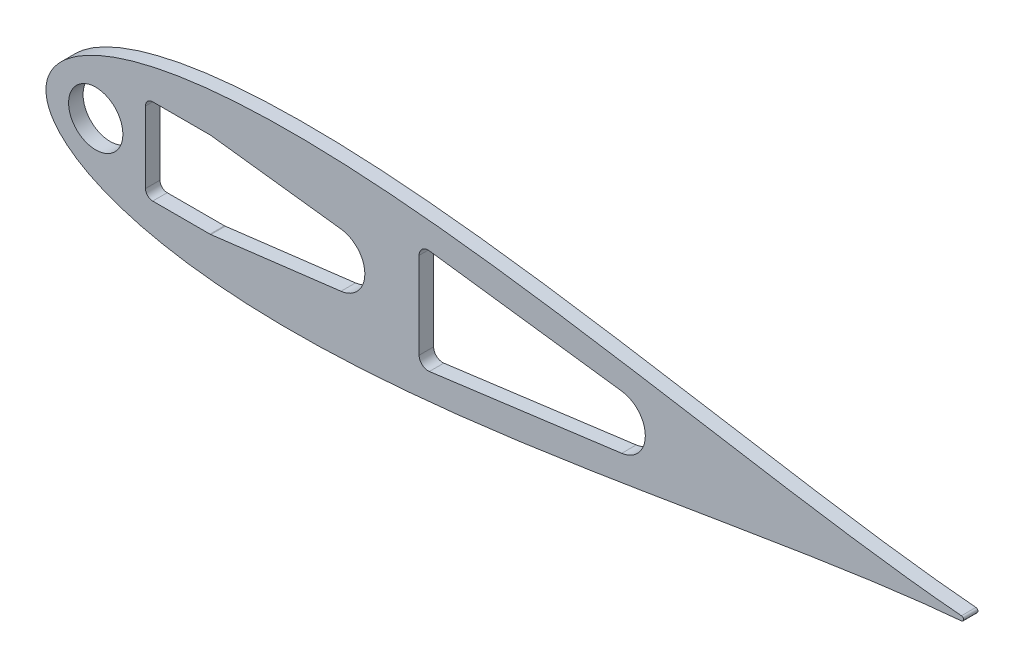
SolidWorks part; units mm, degrees
ref_plane "Front Plane" through (0, 0, 0) normal (0, 0, 1) x (1, 0, 0)
ref_plane "Top Plane" through (0, 0, 0) normal (0, 1, 0) x (1, 0, 0)
ref_plane "Right Plane" through (0, 0, 0) normal (1, 0, 0) x (0, 0, -1)
curve "Curve4"
  spline degree 3 poles (100, 0, 0) (99.8498, 0.0023, 0) (99.4759, 0.008, 0) (99.1023, 0.0238, 0) (98.8789, 0.0332, 0) knots 0 0 0 0 0.401829 1 1 1 1
curve "Curve5"
  spline degree 3 poles (99.3714, -0.0082, 0) (100.2526, 0, 0) (99.3714, 0.0082, 0) (98.8504, 0.035, 0) (97.904, 0.0811, 0) (96.8285, 0.1543, 0) (95.5159, 0.2583, 0) (94.013, 0.3972, 0) (92.313, 0.574, 0) (90.4281, 0.791, 0) (88.3655, 1.0495, 0) (86.1348, 1.3497, 0) (83.7456, 1.691, 0) (81.2082, 2.0715, 0) (78.5335, 2.4886, 0) (75.7326, 2.9386, 0) (72.8172, 3.4168, 0) (69.799, 3.9177, 0) (66.6904, 4.435, 0) (63.5039, 4.9616, 0) (60.2521, 5.4899, 0) (56.948, 6.0119, 0) (53.6049, 6.519, 0) (50.2363, 7.0024, 0) (46.8558, 7.4534, 0) (43.4774, 7.8632, 0) (40.1152, 8.2232, 0) (36.7837, 8.5249, 0) (33.4975, 8.7606, 0) (30.2716, 8.923, 0) (27.1211, 9.0055, 0) (24.0614, 9.0025, 0) (21.108, 8.909, 0) (18.277, 8.7213, 0) (15.5843, 8.4369, 0) (13.0466, 8.0543, 0) (10.6806, 7.5735, 0) (8.5039, 6.996, 0) (6.5349, 6.3253, 0) (4.7933, 5.5673, 0) (3.3001, 4.7321, 0) (2.0777, 3.8366, 0) (1.1467, 2.91, 0) (0.5165, 2.0014, 0) (0.165, 1.1816, 0) (0.0231, 0.524, 0) (-0.0093, 0, 0) (0.0231, -0.524, 0) (0.165, -1.1816, 0) (0.5165, -2.0014, 0) (1.1467, -2.91, 0) (2.0777, -3.8366, 0) (3.3001, -4.7321, 0) (4.7933, -5.5673, 0) (6.5349, -6.3253, 0) (8.5039, -6.996, 0) (10.6806, -7.5735, 0) (13.0466, -8.0543, 0) (15.5843, -8.4369, 0) (18.277, -8.7213, 0) (21.108, -8.909, 0) (24.0614, -9.0025, 0) (27.1211, -9.0055, 0) (30.2716, -8.923, 0) (33.4975, -8.7606, 0) (36.7837, -8.5249, 0) (40.1152, -8.2232, 0) (43.4774, -7.8632, 0) (46.8558, -7.4534, 0) (50.2363, -7.0024, 0) (53.6049, -6.519, 0) (56.948, -6.0119, 0) (60.2521, -5.4899, 0) (63.5039, -4.9616, 0) (66.6904, -4.435, 0) (69.799, -3.9177, 0) (72.8172, -3.4168, 0) (75.7326, -2.9386, 0) (78.5335, -2.4886, 0) (81.2082, -2.0715, 0) (83.7456, -1.691, 0) (86.1348, -1.3497, 0) (88.3655, -1.0495, 0) (90.4281, -0.791, 0) (92.313, -0.574, 0) (94.013, -0.3972, 0) (95.5159, -0.2583, 0) (96.8285, -0.1543, 0) (97.904, -0.0811, 0) (98.8504, -0.035, 0) (99.3714, -0.0082, 0) (100.2526, 0, 0) (99.3714, 0.0082, 0) knots -0.009667 -0.005395 -0.002168 0 0.002168 0.005395 0.009667 0.014967 0.021271 0.028553 0.036781 0.04592 0.055932 0.066773 0.078397 0.090755 0.103793 0.117456 0.131686 0.146422 0.1616 0.177156 0.193024 0.209135 0.225421 0.241812 0.258238 0.274629 0.290914 0.307025 0.322893 0.338448 0.353626 0.368361 0.38259 0.396253 0.40929 0.421647 0.43327 0.444109 0.454119 0.463255 0.471479 0.478755 0.485052 0.490344 0.49461 0.497833 0.5 0.502167 0.50539 0.509656 0.514948 0.521245 0.528521 0.536745 0.545881 0.555891 0.56673 0.578353 0.59071 0.603747 0.61741 0.631639 0.646374 0.661552 0.677107 0.692975 0.709086 0.725371 0.741762 0.758188 0.774579 0.790865 0.806976 0.822844 0.8384 0.853578 0.868314 0.882544 0.896207 0.909245 0.921603 0.933227 0.944068 0.95408 0.963219 0.971447 0.978729 0.985033 0.990333 0.994605 0.997832 1 1.002168 1.005395 1.009667 periodic
sketch "Sketch2" plane through (0, 0, 0) normal (0, 0, 1) x (1, 0, 0)
  line L0 (642.3793, 0) -> (0, 0) construction
  circle A14 centre (642.3793, 0) radius 1.5875 construction
  arc A15 (642.5108, -1.582) -> (642.5108, 1.582) centre (642.3793, 0) ccw
  spline S2 degree 3 poles (666.3448, -0.0547) (672.2538, 0) (666.3448, 0.0547) (662.8509, 0.2344) (656.505, 0.5436) (649.293, 1.0348) (640.4916, 1.7319) (630.4138, 2.6634) (619.0141, 3.8493) (606.375, 5.3044) (592.5439, 7.0376) (577.5855, 9.0506) (561.5643, 11.3389) (544.5497, 13.8907) (526.6141, 16.6877) (507.8326, 19.7051) (488.2827, 22.9117) (468.0444, 26.2704) (447.1994, 29.739) (425.8316, 33.2703) (404.0263, 36.8132) (381.8707, 40.3133) (359.4533, 43.7135) (336.8645, 46.9554) (314.1962, 49.9798) (291.5418, 52.7277) (268.9963, 55.1412) (246.6566, 57.1646) (224.6209, 58.7452) (202.9892, 59.8341) (181.8631, 60.3875) (161.3458, 60.367) (141.542, 59.7399) (122.5581, 58.4818) (104.5023, 56.5743) (87.485, 54.0089) (71.6197, 50.7848) (57.0237, 46.9125) (43.8205, 42.415) (32.1416, 37.3322) (22.1291, 31.7315) (13.9324, 25.7264) (7.6896, 19.5132) (3.4631, 13.4204) (1.1063, 7.9234) (0.1546, 3.5138) (-0.0622, 0) (0.1546, -3.5138) (1.1063, -7.9234) (3.4631, -13.4204) (7.6896, -19.5132) (13.9324, -25.7264) (22.1291, -31.7315) (32.1416, -37.3322) (43.8205, -42.415) (57.0237, -46.9125) (71.6197, -50.7848) (87.485, -54.0089) (104.5023, -56.5743) (122.5581, -58.4818) (141.542, -59.7399) (161.3458, -60.367) (181.8631, -60.3875) (202.9892, -59.8341) (224.6209, -58.7452) (246.6566, -57.1646) (268.9963, -55.1412) (291.5418, -52.7277) (314.1962, -49.9798) (336.8645, -46.9554) (359.4533, -43.7135) (381.8707, -40.3133) (404.0263, -36.8132) (425.8316, -33.2703) (447.1994, -29.739) (468.0444, -26.2704) (488.2827, -22.9117) (507.8326, -19.7051) (526.6141, -16.6877) (544.5497, -13.8907) (561.5643, -11.3389) (577.5855, -9.0506) (592.5439, -7.0376) (606.375, -5.3044) (619.0141, -3.8493) (630.4138, -2.6634) (640.4916, -1.7319) (649.293, -1.0348) (656.505, -0.5436) (662.8509, -0.2344) (666.3448, -0.0547) (672.2538, 0) (666.3448, 0.0547) knots -0.009667 -0.005395 -0.002168 0 0.002168 0.005395 0.009667 0.014967 0.021271 0.028553 0.036781 0.04592 0.055932 0.066773 0.078397 0.090755 0.103793 0.117456 0.131686 0.146422 0.1616 0.177156 0.193024 0.209135 0.225421 0.241812 0.258238 0.274629 0.290914 0.307025 0.322893 0.338448 0.353626 0.368361 0.38259 0.396253 0.40929 0.421647 0.43327 0.444109 0.454119 0.463255 0.471479 0.478755 0.485052 0.490344 0.49461 0.497833 0.5 0.502167 0.50539 0.509656 0.514948 0.521245 0.528521 0.536745 0.545881 0.555891 0.56673 0.578353 0.59071 0.603747 0.61741 0.631639 0.646374 0.661552 0.677107 0.692975 0.709086 0.725371 0.741762 0.758188 0.774579 0.790865 0.806976 0.822844 0.8384 0.853578 0.868314 0.882544 0.896207 0.909245 0.921603 0.933227 0.944068 0.95408 0.963219 0.971447 0.978729 0.985033 0.990333 0.994605 0.997832 1 1.002168 1.005395 1.009667 only from (670.56, 0) to (670.56, 0)
  point P8 (1.2169, -4.6585)
  point P10 (1.2169, 4.6585)
  dimension "D10" = 3.175
extrude "Boss-Extrude1" add sketch "Sketch2" along normal blind 5.4737
extrude "Cut-Extrude4" cut sketch "Sketch7" against normal through all
sketch "Sketch7" plane through (327.9592, -13.7514, 6.35) normal (0, 0, 1) x (1, 0, 0)
  line L1 (-154.9852, -16.7286) -> (-66.0852, -16.7286)
  line L2 (-154.9852, -16.7286) -> (-154.9852, 44.2314)
  line L3 (-154.9852, 44.2314) -> (-66.0852, 44.2314)
  line L4 (-66.0852, -16.7286) -> (-66.0852, 44.2314)
  line L5 (-154.9852, -16.7286) -> (-66.0852, 44.2314) construction
  line L6 (-154.9852, 44.2314) -> (-66.0852, -16.7286) construction
  point P0 (-110.5352, 13.7514)
extrude "Cut-Extrude5" cut sketch "Sketch8" against normal through all
sketch "Sketch8" plane through (327.9592, -13.7514, 6.35) normal (0, 0, 1) x (1, 0, 0)
  circle A0 centre (314.9285, 13.7514) radius 1.2446
scale "Scale1" bodies to scale 101 scale about origin uniform scaling yes scale factor 0.5
sketch "Sketch11" plane through (0, 0, 0) normal (0, 0, -1) x (-1, 0, 0)
  arc A1 (-321.2554, 0.791) -> (-321.2554, -0.791) centre (-321.1896, 0) ccw
  arc A2 (-321.2554, 0.791) -> (-321.2554, -0.791) centre (-321.1896, 0) ccw
  spline S1 degree 3 poles (1670.0286, -183.7614) (-460.597, -6.2387) (-382.8131, 4.917) (-315.2069, -1.3317) (-309.5071, -1.9246) (-303.1875, -2.6522) (-296.272, -3.5188) (-288.7927, -4.5253) (-280.7821, -5.6695) (-272.2749, -6.9453) (-263.3071, -8.3439) (-253.9163, -9.8526) (-244.1414, -11.4558) (-234.0222, -13.1352) (-223.5997, -14.8695) (-212.9158, -16.6352) (-202.0132, -18.4066) (-190.9353, -20.1566) (-179.7267, -21.8568) (-168.4323, -23.4777) (-157.0981, -24.9899) (-145.7709, -26.3639) (-134.4982, -27.5706) (-123.3283, -28.5823) (-112.3104, -29.3726) (-101.4946, -29.9171) (-90.9316, -30.1938) (-80.6729, -30.1835) (-70.771, -29.8699) (-61.2791, -29.2409) (-52.2512, -28.2872) (-43.7425, -27.0045) (-35.8098, -25.3924) (-28.5119, -23.4563) (-21.9102, -21.2075) (-16.0708, -18.6661) (-11.0646, -15.8657) (-6.9662, -12.8632) (-3.8448, -9.7566) (-1.7316, -6.7102) (-0.5532, -3.9617) (-0.0773, -1.7569) (0.0311, 0) (-0.0773, 1.7569) (-0.5532, 3.9617) (-1.7316, 6.7102) (-3.8448, 9.7566) (-6.9662, 12.8632) (-11.0646, 15.8657) (-16.0708, 18.6661) (-21.9102, 21.2075) (-28.5119, 23.4563) (-35.8098, 25.3924) (-43.7425, 27.0045) (-52.2512, 28.2872) (-61.2791, 29.2409) (-70.771, 29.8699) (-80.6729, 30.1835) (-90.9316, 30.1938) (-101.4946, 29.9171) (-112.3104, 29.3726) (-123.3283, 28.5823) (-134.4982, 27.5706) (-145.7709, 26.3639) (-157.0981, 24.9899) (-168.4323, 23.4777) (-179.7267, 21.8568) (-190.9353, 20.1566) (-202.0132, 18.4066) (-212.9158, 16.6352) (-223.5997, 14.8695) (-234.0222, 13.1352) (-244.1414, 11.4558) (-253.9163, 9.8526) (-263.3071, 8.3439) (-272.2749, 6.9453) (-280.7821, 5.6695) (-288.7927, 4.5253) (-296.272, 3.5188) (-303.1875, 2.6522) (-309.5071, 1.9246) (-315.2069, 1.3317) (-382.8156, -4.9172) (-460.6028, 6.2395) (1670.2753, 183.7819) knots -0.255895 -0.255895 -0.255895 -0.255895 0.021271 0.028553 0.036781 0.04592 0.055932 0.066773 0.078397 0.090755 0.103793 0.117456 0.131686 0.146422 0.1616 0.177156 0.193024 0.209135 0.225421 0.241812 0.258238 0.274629 0.290914 0.307025 0.322893 0.338448 0.353626 0.368361 0.38259 0.396253 0.40929 0.421647 0.43327 0.444109 0.454119 0.463255 0.471479 0.478755 0.485052 0.490344 0.49461 0.497833 0.5 0.502167 0.50539 0.509656 0.514948 0.521245 0.528521 0.536745 0.545881 0.555891 0.56673 0.578353 0.59071 0.603747 0.61741 0.631639 0.646374 0.661552 0.677107 0.692975 0.709086 0.725371 0.741762 0.758188 0.774579 0.790865 0.806976 0.822844 0.8384 0.853578 0.868314 0.882544 0.896207 0.909245 0.921603 0.933227 0.944068 0.95408 0.963219 0.971447 0.978729 1.255906 1.255906 1.255906 1.255906 only from (-321.2554, -0.791) to (-321.2554, 0.791)
  spline S2 degree 3 poles (-321.2554, -0.791) (-320.9967, -0.8125) (-319.0469, -0.9768) (-315.2069, -1.3317) (-309.5071, -1.9246) (-303.1875, -2.6522) (-296.272, -3.5188) (-288.7927, -4.5253) (-280.7821, -5.6695) (-272.2749, -6.9453) (-263.3071, -8.3439) (-253.9163, -9.8526) (-244.1414, -11.4558) (-234.0222, -13.1352) (-223.5997, -14.8695) (-212.9158, -16.6352) (-202.0132, -18.4066) (-190.9353, -20.1566) (-179.7267, -21.8568) (-168.4323, -23.4777) (-157.0981, -24.9899) (-145.7709, -26.3639) (-134.4982, -27.5706) (-123.3283, -28.5823) (-112.3104, -29.3726) (-101.4946, -29.9171) (-90.9316, -30.1938) (-80.6729, -30.1835) (-70.771, -29.8699) (-61.2791, -29.2409) (-52.2512, -28.2872) (-43.7425, -27.0045) (-35.8098, -25.3924) (-28.5119, -23.4563) (-21.9102, -21.2075) (-16.0708, -18.6661) (-11.0646, -15.8657) (-6.9662, -12.8632) (-3.8448, -9.7566) (-1.7316, -6.7102) (-0.5532, -3.9617) (-0.0773, -1.7569) (0.0311, 0) (-0.0773, 1.7569) (-0.5532, 3.9617) (-1.7316, 6.7102) (-3.8448, 9.7566) (-6.9662, 12.8632) (-11.0646, 15.8657) (-16.0708, 18.6661) (-21.9102, 21.2075) (-28.5119, 23.4563) (-35.8098, 25.3924) (-43.7425, 27.0045) (-52.2512, 28.2872) (-61.2791, 29.2409) (-70.771, 29.8699) (-80.6729, 30.1835) (-90.9316, 30.1938) (-101.4946, 29.9171) (-112.3104, 29.3726) (-123.3283, 28.5823) (-134.4982, 27.5706) (-145.7709, 26.3639) (-157.0981, 24.9899) (-168.4323, 23.4777) (-179.7267, 21.8568) (-190.9353, 20.1566) (-202.0132, 18.4066) (-212.9158, 16.6352) (-223.5997, 14.8695) (-234.0222, 13.1352) (-244.1414, 11.4558) (-253.9163, 9.8526) (-263.3071, 8.3439) (-272.2749, 6.9453) (-280.7821, 5.6695) (-288.7927, 4.5253) (-296.272, 3.5188) (-303.1875, 2.6522) (-309.5071, 1.9246) (-315.2069, 1.3317) (-319.0469, 0.9768) (-320.9967, 0.8125) (-321.2554, 0.791) knots 0.020157 0.020157 0.020157 0.020157 0.021271 0.028553 0.036781 0.04592 0.055932 0.066773 0.078397 0.090755 0.103793 0.117456 0.131686 0.146422 0.1616 0.177156 0.193024 0.209135 0.225421 0.241812 0.258238 0.274629 0.290914 0.307025 0.322893 0.338448 0.353626 0.368361 0.38259 0.396253 0.40929 0.421647 0.43327 0.444109 0.454119 0.463255 0.471479 0.478755 0.485052 0.490344 0.49461 0.497833 0.5 0.502167 0.50539 0.509656 0.514948 0.521245 0.528521 0.536745 0.545881 0.555891 0.56673 0.578353 0.59071 0.603747 0.61741 0.631639 0.646374 0.661552 0.677107 0.692975 0.709086 0.725371 0.741762 0.758188 0.774579 0.790865 0.806976 0.822844 0.8384 0.853578 0.868314 0.882544 0.896207 0.909245 0.921603 0.933227 0.944068 0.95408 0.963219 0.971447 0.978729 0.979843 0.979843 0.979843 0.979843
  dimension "D1" = 0
extrude "Boss-Extrude2" add sketch "Sketch11" against normal blind 5.08
sketch "Sketch10" plane through (0, 0, 0) normal (0, 0, 1) x (1, 0, 0)
  line L1 (34.925, -15.0812) -> (60.0922, -15.0812)
  line L2 (34.925, -15.0812) -> (34.925, 15.0812)
  line L3 (34.925, 15.0812) -> (60.0922, 15.0812)
  line L4 (60.0922, -15.0812) -> (60.0922, 15.0812)
  line L5 (34.925, -15.0812) -> (60.0922, 15.0812) construction
  line L6 (34.925, 15.0812) -> (60.0922, -15.0812) construction
  arc A2 (321.2554, -0.791) -> (321.2554, 0.791) centre (321.1896, 0) ccw
  arc A3 (321.2554, -0.791) -> (321.2554, 0.791) centre (321.1896, 0) ccw construction
  spline S1 degree 3 poles (-673.8168, 99.1117) (432.0128, 2.6778) (370.563, -3.7848) (315.2069, 1.3317) (309.5071, 1.9246) (303.1875, 2.6522) (296.272, 3.5188) (288.7927, 4.5253) (280.7821, 5.6695) (272.2749, 6.9453) (263.3071, 8.3439) (253.9163, 9.8526) (244.1414, 11.4558) (234.0222, 13.1352) (223.5997, 14.8695) (212.9158, 16.6352) (202.0132, 18.4066) (190.9353, 20.1566) (179.7267, 21.8568) (168.4323, 23.4777) (157.0981, 24.9899) (145.7709, 26.3639) (134.4982, 27.5706) (123.3283, 28.5823) (112.3104, 29.3726) (101.4946, 29.9171) (90.9316, 30.1938) (80.6729, 30.1835) (70.771, 29.8699) (61.2791, 29.2409) (52.2512, 28.2872) (43.7425, 27.0045) (35.8098, 25.3924) (28.5119, 23.4563) (21.9102, 21.2075) (16.0708, 18.6661) (11.0646, 15.8657) (6.9662, 12.8632) (3.8448, 9.7566) (1.7316, 6.7102) (0.5532, 3.9617) (0.0773, 1.7569) (-0.0311, 0) (0.0773, -1.7569) (0.5532, -3.9617) (1.7316, -6.7102) (3.8448, -9.7566) (6.9662, -12.8632) (11.0646, -15.8657) (16.0708, -18.6661) (21.9102, -21.2075) (28.5119, -23.4563) (35.8098, -25.3924) (43.7425, -27.0045) (52.2512, -28.2872) (61.2791, -29.2409) (70.771, -29.8699) (80.6729, -30.1835) (90.9316, -30.1938) (101.4946, -29.9171) (112.3104, -29.3726) (123.3283, -28.5823) (134.4982, -27.5706) (145.7709, -26.3639) (157.0981, -24.9899) (168.4323, -23.4777) (179.7267, -21.8568) (190.9353, -20.1566) (202.0132, -18.4066) (212.9158, -16.6352) (223.5997, -14.8695) (234.0222, -13.1352) (244.1414, -11.4558) (253.9163, -9.8526) (263.3071, -8.3439) (272.2749, -6.9453) (280.7821, -5.6695) (288.7927, -4.5253) (296.272, -3.5188) (303.1875, -2.6522) (309.5071, -1.9246) (315.2069, -1.3317) (370.564, 3.7849) (432.0152, -2.6781) (-673.8821, -99.1174) knots -0.202863 -0.202863 -0.202863 -0.202863 0.021271 0.028553 0.036781 0.04592 0.055932 0.066773 0.078397 0.090755 0.103793 0.117456 0.131686 0.146422 0.1616 0.177156 0.193024 0.209135 0.225421 0.241812 0.258238 0.274629 0.290914 0.307025 0.322893 0.338448 0.353626 0.368361 0.38259 0.396253 0.40929 0.421647 0.43327 0.444109 0.454119 0.463255 0.471479 0.478755 0.485052 0.490344 0.49461 0.497833 0.5 0.502167 0.50539 0.509656 0.514948 0.521245 0.528521 0.536745 0.545881 0.555891 0.56673 0.578353 0.59071 0.603747 0.61741 0.631639 0.646374 0.661552 0.677107 0.692975 0.709086 0.725371 0.741762 0.758188 0.774579 0.790865 0.806976 0.822844 0.8384 0.853578 0.868314 0.882544 0.896207 0.909245 0.921603 0.933227 0.944068 0.95408 0.963219 0.971447 0.978729 1.202867 1.202867 1.202867 1.202867 only from (321.2554, 0.791) to (321.2554, -0.791)
  point P0 (47.5086, 0)
  dimension "D1" = 25.1672
  dimension "D2" = 34.925
  dimension "D5" = 30.1625
  dimension "D3" = 0
extrude "Cut-Extrude6" cut sketch "Sketch10" along normal through all
fillet "Fillet1" radius 2.54 4 edges at (60.0922, -15.0812, 2.54) (34.925, -15.0812, 2.54) (34.925, 15.0812, 2.54) (60.0922, 15.0812, 2.54)
hole_wizard "#8 Clearance Hole1" positions "Sketch12" profile "Sketch13" hole size "#8" standard "ANSI Inch"
sketch "Sketch12" plane through (0, 0, 5.08) normal (0, 0, 1) x (1, 0, 0)
  line L0 (76.2, 0) -> (0, 0) construction
  line L2 (31.75, 8.8646) -> (31.75, -8.8646) construction
  point P0 (12.7, 0)
  point P2 (76.2, 0)
  dimension "D1" = 19.05
  dimension "D2" = 44.45
sketch "Sketch13" plane through (12.7, 0, 5.08) normal (1, 0, 0) x (0, -1, 0)
  line L0 (0, 0) -> (0, 5.08)
  line L1 (0, 5.08) -> (2.2479, 5.08)
  line L2 (2.2479, 5.08) -> (2.2479, 0)
  line L5 (2.2479, 0) -> (0, 0)
  line L11 (0, -6.35) -> (0, 107.95) construction
  dimension "Thru Hole Dia." = 4.4958
  dimension "Thru Hole Depth" = 5.08
sketch "Sketch15" plane through (0, 0, 5.08) normal (0, 0, 1) x (1, 0, 0)
  line L0 (35.6689, 14.3373) -> (59.3482, -14.3373)
  line L1 (24.0679, 12.7) -> (74.8679, -12.7) construction
  line L2 (26.6079, 12.7) -> (72.3279, 12.7)
  line L3 (24.0679, 10.16) -> (24.0679, -10.16)
  line L4 (26.6079, -12.7) -> (72.3279, -12.7)
  line L5 (74.8679, 10.16) -> (74.8679, -10.16)
  circle A0 centre (47.5086, 0) radius 13.716
  arc A1 (37.465, 15.0812) -> (34.925, 12.5412) centre (37.465, 12.5412) ccw construction
  arc A2 (57.5522, -15.0812) -> (60.0922, -12.5412) centre (57.5522, -12.5412) ccw construction
  arc A3 (72.3279, 12.7) -> (74.8679, 10.16) centre (72.3279, 10.16) cw
  arc A4 (74.8679, -10.16) -> (72.3279, -12.7) centre (72.3279, -10.16) cw
  arc A5 (26.6079, -12.7) -> (24.0679, -10.16) centre (26.6079, -10.16) cw
  arc A6 (26.6079, 12.7) -> (24.0679, 10.16) centre (26.6079, 10.16) ccw
  point P10 (49.4679, 0)
  point P18 (74.8679, 12.7)
  dimension "D1" = 27.432
  dimension "D4" = 2.54
  dimension "D2" = 50.8
  dimension "D3" = 25.4
sketch "Sketch16" plane through (0, 0, 5.08) normal (0, 0, 1) x (1, 0, 0)
  line L0 (102.3726, 0) -> (100.5946, 0) construction
  line L1 (102.3726, -9.525) -> (100.5946, -9.525)
  line L2 (102.3726, 9.525) -> (100.5946, 9.525)
  arc A0 (102.3726, -9.525) -> (102.3726, 9.525) centre (102.3726, 0) ccw
  arc A1 (100.5946, 9.525) -> (100.5946, -9.525) centre (100.5946, 0) ccw
  point P3 (101.4836, 0)
  dimension "D1" = 9.525
  dimension "D2" = 1.778
  dimension "D3" = 53.975
extrude "Cut-Extrude8" cut sketch "Sketch16" against normal through all
sketch "Sketch18" plane through (0, 0, 5.08) normal (0, 0, 1) x (1, 0, 0)
  line L2 (57.8617, 15.0623) -> (103.5335, 9.454)
  line L4 (103.5335, -9.454) -> (57.8617, -15.0623)
  line L5 (60.0922, -12.5412) -> (60.0922, 12.5412) construction
  line L8 (60.0922, -12.5412) -> (60.0922, 12.5412)
  arc A0 (60.0922, 12.5412) -> (57.5522, 15.0812) centre (57.5522, 12.5412) ccw construction
  arc A3 (102.3726, -9.525) -> (102.3726, 9.525) centre (102.3726, 0) ccw construction
  arc A4 (57.5522, -15.0812) -> (60.0922, -12.5412) centre (57.5522, -12.5412) ccw construction
  arc A6 (103.5335, -9.454) -> (103.5335, 9.454) centre (102.3726, 0) ccw
  arc A8 (57.8617, -15.0623) -> (60.0922, -12.5412) centre (57.5522, -12.5412) ccw
  arc A9 (60.0922, 12.5412) -> (57.8617, 15.0623) centre (57.5522, 12.5412) ccw
extrude "Cut-Extrude9" cut sketch "Sketch18" against normal through all
sketch "Sketch19" plane through (0, 0, 5.08) normal (0, 0, 1) x (1, 0, 0)
  line L0 (0, 0) -> (34.925, 0) construction
  line L1 (34.925, 12.5412) -> (34.925, -12.5412) construction
  line L2 (130.9476, 15.1827) -> (130.9476, -15.1827)
  line L3 (134.537, -18.3306) -> (202.0408, -9.4435)
  line L4 (202.0408, 9.4435) -> (134.537, 18.3306)
  arc A0 (103.5335, -9.454) -> (103.5335, 9.454) centre (102.3726, 0) ccw construction
  circle A1 centre (17.4625, 0) radius 9.525
  arc A2 (202.0408, -9.4435) -> (202.0408, 9.4435) centre (200.7976, 0) ccw
  arc A3 (134.537, -18.3306) -> (130.9476, -15.1827) centre (134.1226, -15.1827) cw
  arc A4 (130.9476, 15.1827) -> (134.537, 18.3306) centre (134.1226, 15.1827) cw
  point P16 (0, 0)
  point P17 (130.9476, 0)
  point P18 (0, 0)
  point P22 (111.8976, 0)
  dimension "D1" = 19.05
  dimension "D2" = 9.525
  dimension "D3" = 3.175
  dimension "D4" = 3.175
  dimension "D5" = 15
  dimension "D6" = 19.05
  dimension "D7" = 88.9
extrude "Cut-Extrude10" cut sketch "Sketch19" against normal through all
equation "\"0.5n\"=0"
equation "\"D1@Sketch10\"=0.898/cos(25deg)"
